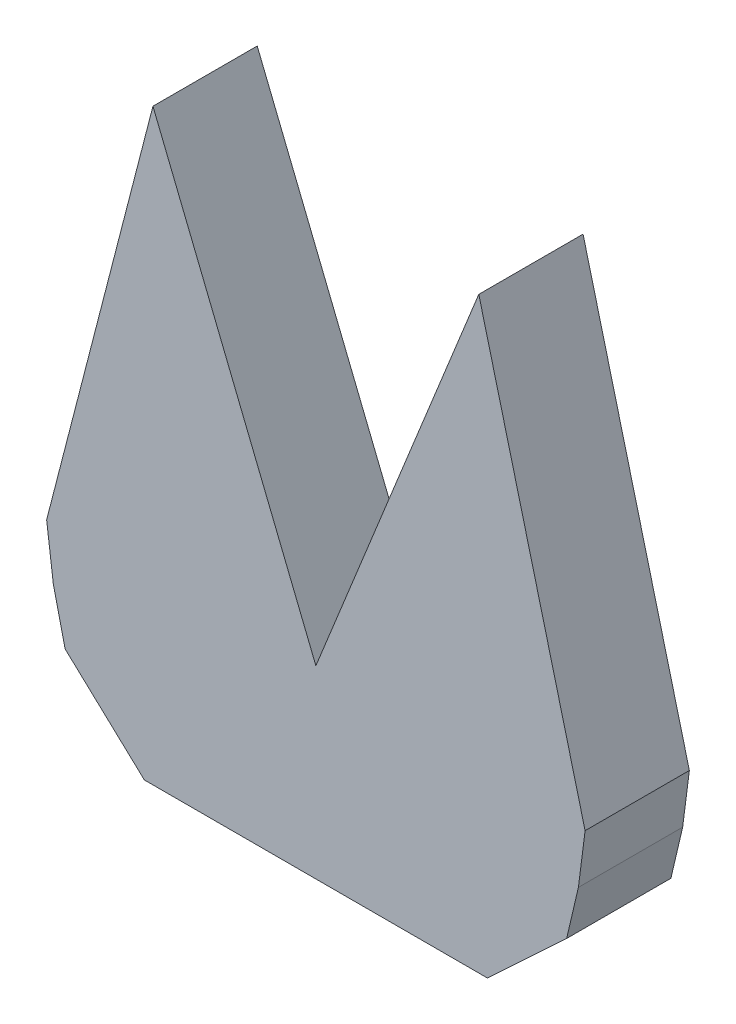
SolidWorks part; units mm, degrees
ref_plane "Front Plane" through (0, 0, 0) normal (0, 0, 1) x (1, 0, 0)
ref_plane "Top Plane" through (0, 0, 0) normal (0, 1, 0) x (1, 0, 0)
ref_plane "Right Plane" through (0, 0, 0) normal (1, 0, 0) x (0, 0, -1)
sketch "Sketch2" plane through (0, 0, 0) normal (0, 0, 1) x (1, 0, 0)
  line L0 (0, 165.0238) -> (0, -71.5015) construction
  line L1 (-30, 0) -> (30, 0)
  line L2 (30, 0) -> (57.7249, 16.9965)
  line L3 (57.7249, 16.9965) -> (61.9749, 40.6172)
  line L4 (61.9749, 40.6172) -> (37.5043, 135.3063)
  line L5 (37.5043, 135.3063) -> (0, 42.5085)
  line L6 (-30, 0) -> (-57.7249, 16.9965)
  line L7 (-57.7249, 16.9965) -> (-61.9749, 40.6172)
  line L8 (-61.9749, 40.6172) -> (-37.5043, 135.3063)
  line L9 (-37.5043, 135.3063) -> (0, 42.5085)
  point P11 (0, 0)
  dimension "D1" = 30
  dimension "D2" = 32.52
  dimension "D3" = 24
  dimension "D4" = 97.8
  dimension "D5" = 100.09
  dimension "D6" = 211.51
  dimension "D7" = 228.29
  dimension "D8" = 204.69
  dimension "D9" = 143.504
sketch "Sketch3" plane through (0, 0, 0) normal (0, 0, 1) x (1, 0, 0)
  line L0 (39.48, 0) -> (-39.48, 0)
  line L1 (-39.48, 0) -> (-60.4332, 28.5452)
  line L2 (-60.4332, 28.5452) -> (-56.6, 52.2371)
  line L3 (-56.6, 52.2371) -> (-2.08, 133.4308)
  line L4 (-2.08, 133.4308) -> (2.08, 133.4308)
  line L5 (0, 200165.0238) -> (0, -200071.5015) construction
  line L6 (0, 164.8965) -> (0, -16.5935) construction
  line L7 (39.48, 0) -> (60.4332, 28.5452)
  line L8 (60.4332, 28.5452) -> (56.6, 52.2371)
  line L9 (56.6, 52.2371) -> (2.08, 133.4308)
  point P12 (0, 0)
  point P15 (0, 133.4308)
  dimension "D1" = 39.48
  dimension "D2" = 35.41
  dimension "D3" = 24
  dimension "D4" = 97.8
  dimension "D5" = 2.08
  dimension "D6" = 233.72
  dimension "D7" = 204.69
  dimension "D8" = 45.471
  dimension "D9" = 56.119
sketch "Sketch4" plane through (0, 0, 0) normal (0, 0, 1) x (1, 0, 0)
  line L0 (39.48, 0) -> (-39.48, 0)
  line L1 (-39.48, 0) -> (-57.7249, 16.9965)
  line L2 (-57.7249, 16.9965) -> (-60.4332, 28.5452)
  line L3 (-60.4332, 28.5452) -> (-61.9749, 40.6172)
  line L4 (-61.9749, 40.6172) -> (-37.5043, 135.3063)
  line L5 (-37.5043, 135.3063) -> (0, 42.5085)
  line L6 (0, 164.8965) -> (0, -16.5935) construction
  line L7 (39.48, 0) -> (57.7249, 16.9965)
  line L8 (57.7249, 16.9965) -> (60.4332, 28.5452)
  line L9 (60.4332, 28.5452) -> (61.9749, 40.6172)
  line L10 (61.9749, 40.6172) -> (37.5043, 135.3063)
  line L11 (37.5043, 135.3063) -> (0, 42.5085)
  point P19 (0, 0)
extrude "Boss-Extrude1" add sketch "Sketch4" along normal blind 24
